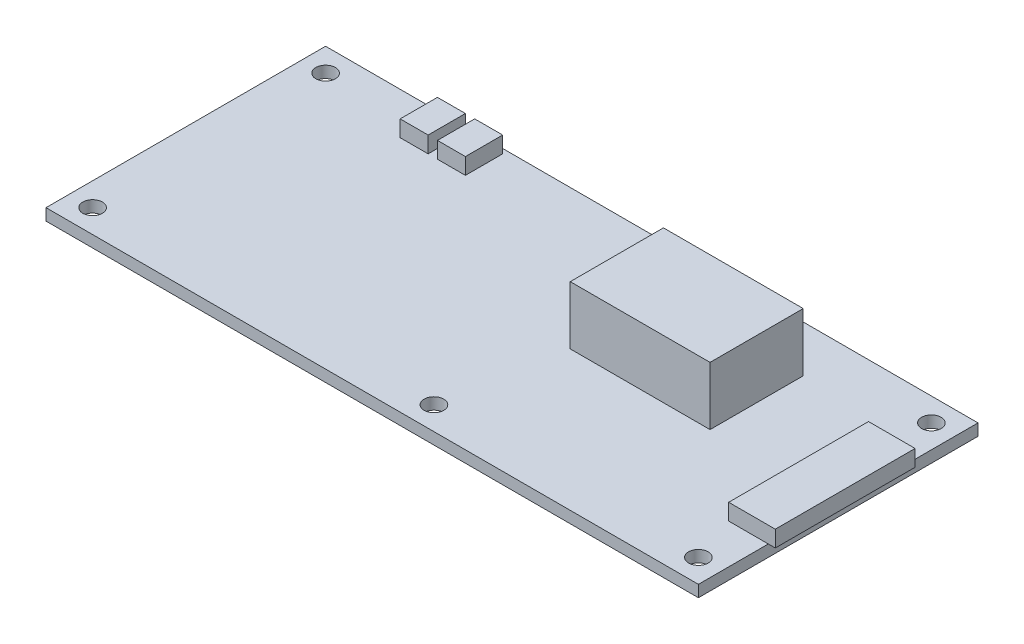
SolidWorks part; units mm, degrees
ref_plane "Front Plane" through (0, 0, 0) normal (0, 0, 1) x (1, 0, 0)
ref_plane "Top Plane" through (0, 0, 0) normal (0, 1, 0) x (1, 0, 0)
ref_plane "Right Plane" through (0, 0, 0) normal (1, 0, 0) x (0, 0, -1)
sketch "Sketch2" plane through (0, 0, 0) normal (0, 1, 0) x (1, 0, 0)
  line L1 (-70, 30) -> (70, 30)
  line L2 (-70, 30) -> (-70, -30)
  line L3 (-70, -30) -> (70, -30)
  line L4 (70, 30) -> (70, -30)
  line L5 (-70, 30) -> (70, -30) construction
  line L6 (-70, -30) -> (70, 30) construction
  circle A0 centre (-65, 25) radius 2.1
  circle A1 centre (8.25, 25) radius 2.1
  circle A2 centre (65, 25) radius 2.1
  circle A3 centre (-65, -25) radius 2.1
  circle A4 centre (8.25, -25) radius 2.1
  circle A5 centre (65, -25) radius 2.1
  point P0 (0, 0)
  dimension "D3" = 4.2
  dimension "D1" = 140
  dimension "D2" = 60
  dimension "D4" = 5
  dimension "D5" = 5
  dimension "D6" = 5
  dimension "D7" = 78.25
  dimension "D8" = 135
extrude "Boss-Extrude1" add sketch "Sketch2" along normal blind 2.5
sketch "Sketch3" plane through (0, 2.5, 0) normal (0, 1, 0) x (1, 0, 0)
  line L0 (70, -30) -> (70, 30) construction
  line L1 (-45, 29) -> (-39, 29)
  line L2 (-45, 29) -> (-45, 21)
  line L3 (-45, 21) -> (-39, 21)
  line L4 (-39, 29) -> (-39, 21)
  line L5 (-37, 29) -> (-31, 29)
  line L6 (-37, 29) -> (-37, 21)
  line L7 (-37, 21) -> (-31, 21)
  line L8 (-31, 29) -> (-31, 21)
  line L9 (70, 30) -> (-70, 30) construction
  line L10 (-70, 30) -> (-70, -30) construction
  line L13 (61.5, 15) -> (71.5, 15)
  line L14 (61.5, 15) -> (61.5, -15)
  line L15 (61.5, -15) -> (71.5, -15)
  line L16 (71.5, 15) -> (71.5, -15)
  point P18 (70, 0)
  point P19 (61.5, 0)
  dimension "D1" = 1.5
  dimension "D2" = 8.5
  dimension "D3" = 30
  dimension "D4" = 1
  dimension "D5" = 2
  dimension "D6" = 25
  dimension "D7" = 8
  dimension "D8" = 6
extrude "Boss-Extrude2" add sketch "Sketch3" along normal blind 3.5
sketch "Sketch4" plane through (0, 2.5, 0) normal (0, 1, 0) x (1, 0, 0)
  line L0 (-70, 30) -> (-70, -30) construction
  line L1 (12.5, 20) -> (42.5, 20)
  line L2 (12.5, 20) -> (12.5, 0)
  line L3 (12.5, 0) -> (42.5, 0)
  line L4 (42.5, 20) -> (42.5, 0)
  line L5 (70, 30) -> (-70, 30) construction
  dimension "D1" = 82.5
  dimension "D2" = 10
  dimension "D3" = 30
  dimension "D4" = 20
extrude "Boss-Extrude3" add sketch "Sketch4" along normal blind 12.5
